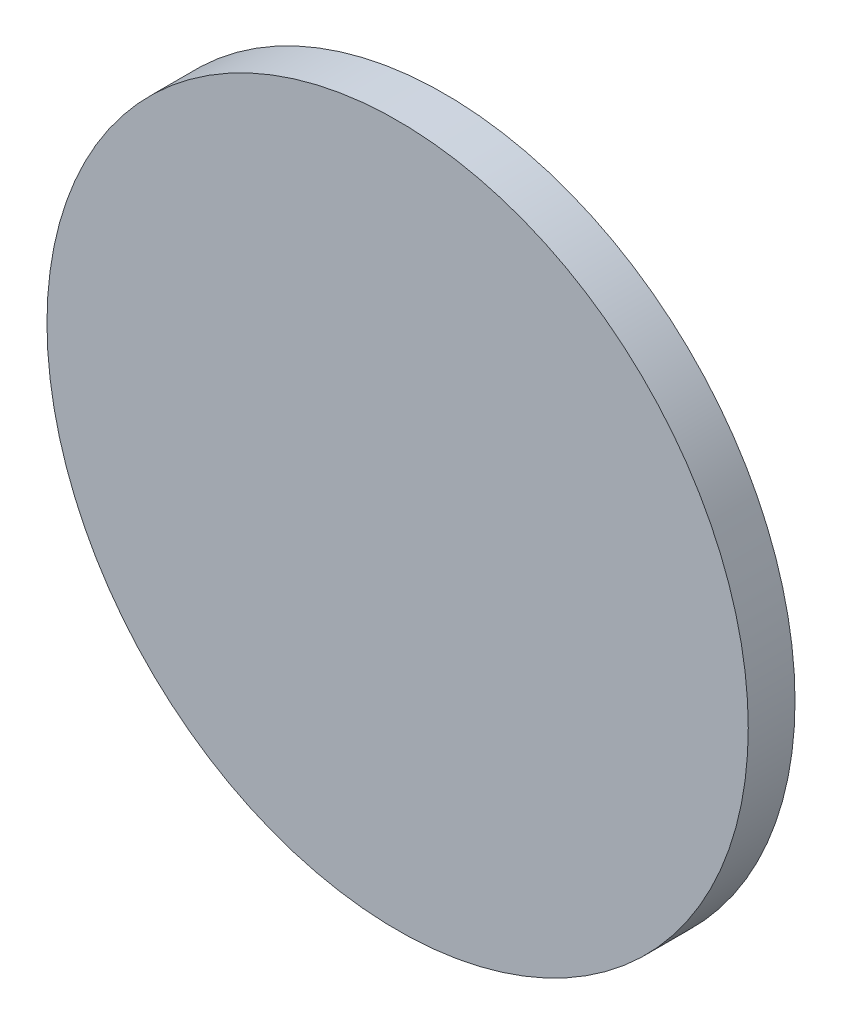
SolidWorks part; units mm, degrees
material "1023 Carbon Steel Sheet (SS)"
ref_plane "Front Plane" through (0, 0, 0) normal (0, 0, 1) x (1, 0, 0)
ref_plane "Top Plane" through (0, 0, 0) normal (0, 1, 0) x (1, 0, 0)
ref_plane "Right Plane" through (0, 0, 0) normal (1, 0, 0) x (0, 0, -1)
sketch "Sketch2" plane through (0, 0, 0) normal (0, 0, 1) x (1, 0, 0)
  circle A0 centre (0, 0) radius 22.5
extrude "Boss-Extrude1" add sketch "Sketch2" along normal blind 3
